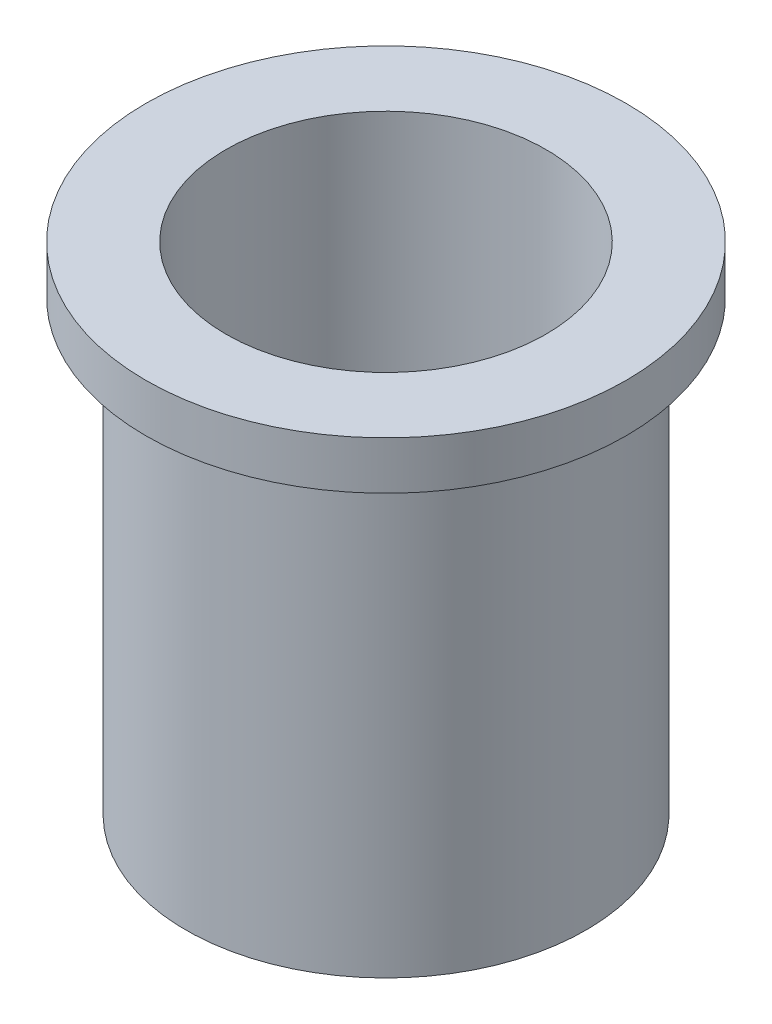
SolidWorks part; units mm, degrees
ref_plane "Front Plane" through (0, 0, 0) normal (0, 0, 1) x (1, 0, 0)
ref_plane "Top Plane" through (0, 0, 0) normal (0, 1, 0) x (1, 0, 0)
ref_plane "Right Plane" through (0, 0, 0) normal (1, 0, 0) x (0, 0, -1)
sketch "Sketch1" plane through (0, 0, 0) normal (0, 1, 0) x (1, 0, 0)
  circle A0 centre (0, 0) radius 15
  dimension "D1" = 30
extrude "Boss-Extrude1" add sketch "Sketch1" along normal mid plane 3
sketch "Sketch2" plane through (0, -1.5, 0) normal (0, -1, 0) x (1, 0, 0)
  circle A0 centre (0, 0) radius 12.5
  dimension "D1" = 25
extrude "Boss-Extrude2" add sketch "Sketch2" along normal blind 28
sketch "Sketch3" plane through (0, 1.5, 0) normal (0, 1, 0) x (1, 0, 0)
  circle A0 centre (0, 0) radius 10
  dimension "D1" = 20
extrude "Cut-Extrude1" cut sketch "Sketch3" against normal through all
